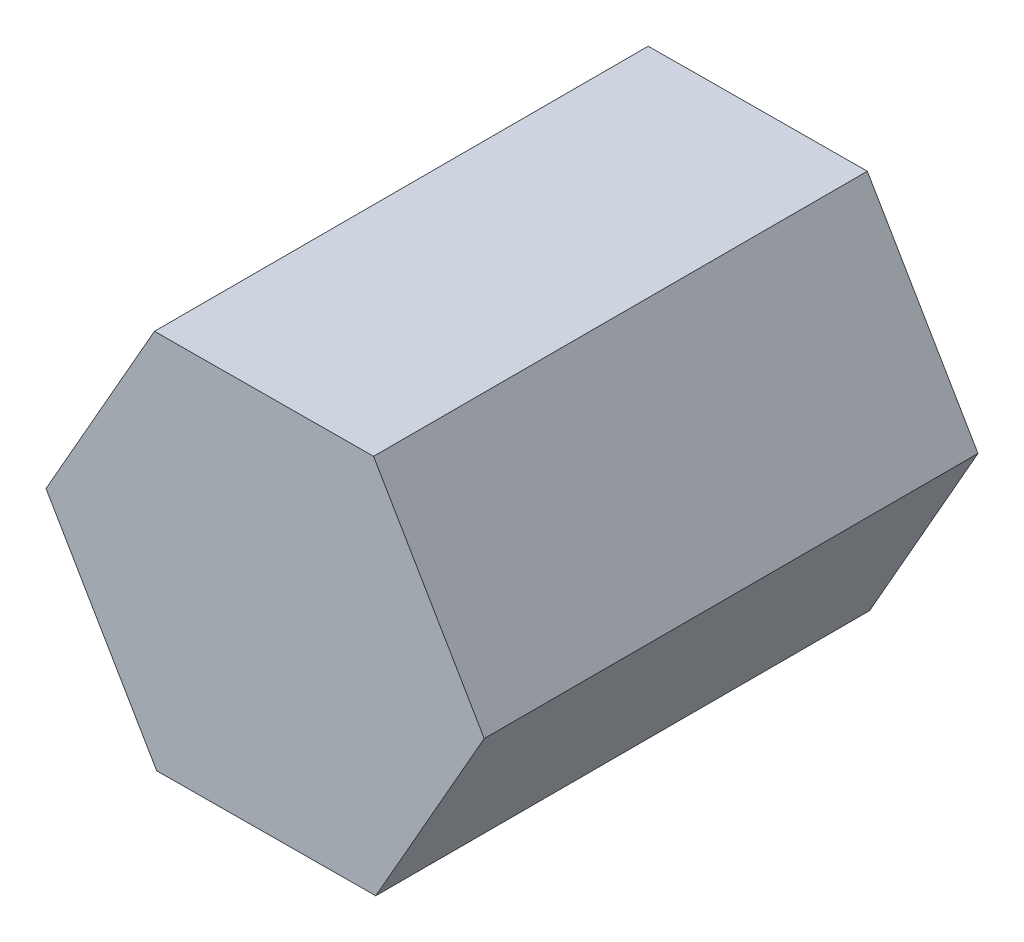
SolidWorks part; units mm, degrees
ref_plane "Piano frontale" through (0, 0, 0) normal (0, 0, 1) x (1, 0, 0)
ref_plane "Piano superiore" through (0, 0, 0) normal (0, 1, 0) x (1, 0, 0)
ref_plane "Piano destro" through (0, 0, 0) normal (1, 0, 0) x (0, 0, -1)
sketch "Schizzo1" plane through (0, 0, 0) normal (0, 0, 1) x (1, 0, 0)
  line L1 (-35.8595, 61.2789) -> (-70.9988, -0.4158)
  line L2 (-70.9988, -0.4158) -> (-35.1393, -61.6946)
  line L3 (-35.1393, -61.6946) -> (35.8595, -61.2789)
  line L4 (35.8595, -61.2789) -> (70.9988, 0.4158)
  line L5 (70.9988, 0.4158) -> (35.1393, 61.6946)
  line L6 (35.1393, 61.6946) -> (-35.8595, 61.2789)
  circle A0 centre (0, 0) radius 61.4878 construction
  dimension "D1" = 71
extrude "Estrusione-Estrusione1" add sketch "Schizzo1" along normal blind 160 contours L1 L2 L3 L4 L5 L6
